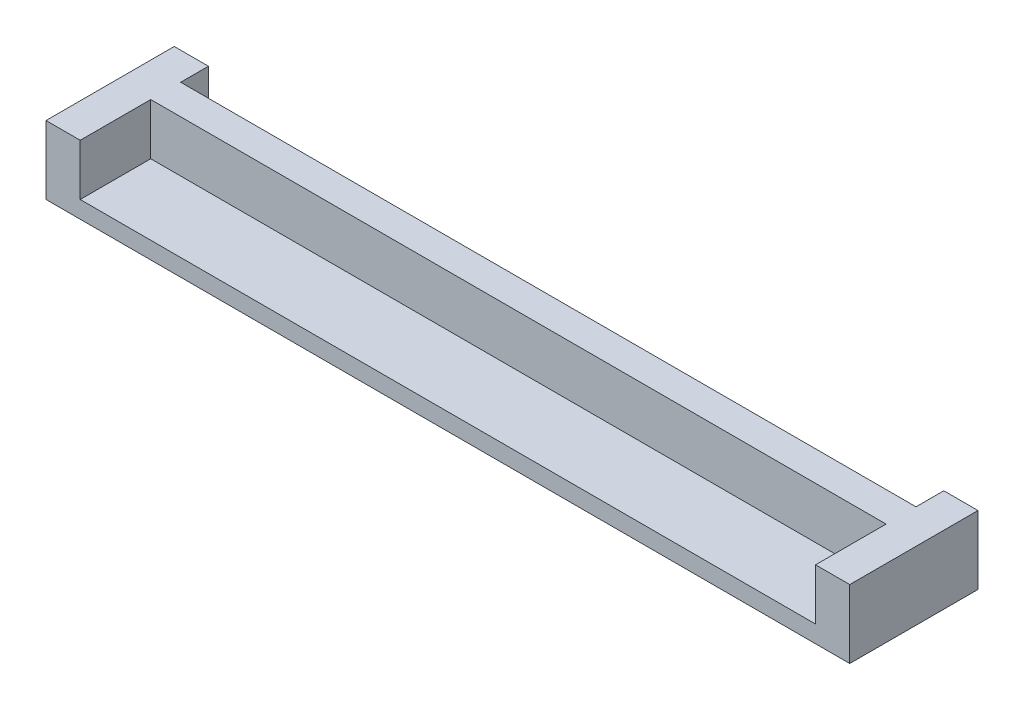
SolidWorks part; units mm, degrees
ref_plane "Front Plane" through (0, 0, 0) normal (0, 0, 1) x (1, 0, 0)
ref_plane "Top Plane" through (0, 0, 0) normal (0, 1, 0) x (1, 0, 0)
ref_plane "Right Plane" through (0, 0, 0) normal (1, 0, 0) x (0, 0, -1)
sketch "Sketch1" plane through (0, 0, 0) normal (0, 1, 0) x (1, 0, 0)
  line L0 (57.1387, 3.4692) -> (151.1387, 3.4692) construction
  line L1 (57.1387, 8.4692) -> (61.1387, 8.4692)
  line L2 (57.1387, 8.4692) -> (57.1387, -6.5308)
  line L3 (57.1387, -6.5308) -> (61.1387, -6.5308)
  line L4 (61.1387, 8.4692) -> (61.1387, 5.2192)
  line L5 (147.1387, 8.4692) -> (151.1387, 8.4692)
  line L6 (147.1387, 8.4692) -> (147.1387, 5.2192)
  line L7 (147.1387, -6.5308) -> (151.1387, -6.5308)
  line L8 (151.1387, 8.4692) -> (151.1387, -6.5308)
  line L9 (61.1387, 5.2192) -> (147.1387, 5.2192)
  line L10 (147.1387, 1.7192) -> (61.1387, 1.7192)
  line L11 (61.1387, 1.7192) -> (61.1387, -6.5308)
  line L12 (147.1387, 1.7192) -> (147.1387, -6.5308)
  point P11 (0, 0)
  point P15 (0, 0)
  point P16 (0, 0)
  point P18 (0, 0)
  dimension "D1" = 4
  dimension "D3" = 4
  dimension "D4" = 15
  dimension "D5" = 10
  dimension "D6" = 3.5
  dimension "D7" = 1.75
extrude "Boss-Extrude1" add sketch "Sketch1" along normal blind 6
sketch "Sketch2" plane through (0, 0, 0) normal (0, -1, 0) x (1, 0, 0)
  line L1 (57.1387, 6.5308) -> (151.1387, 6.5308)
  line L2 (57.1387, 6.5308) -> (57.1387, -8.4692)
  line L3 (57.1387, -8.4692) -> (151.1387, -8.4692)
  line L4 (151.1387, 6.5308) -> (151.1387, -8.4692)
extrude "Boss-Extrude2" add sketch "Sketch2" along normal blind 2
